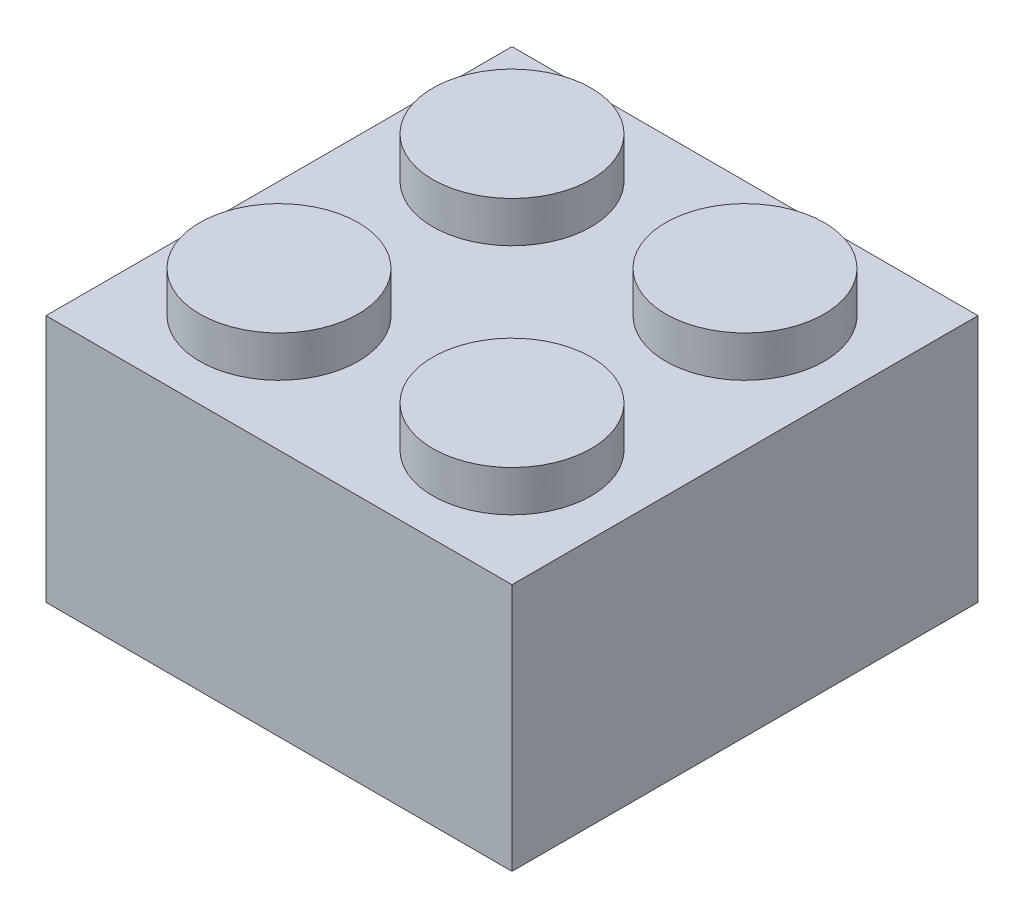
SolidWorks part; units mm, degrees
ref_plane "Front Plane" through (0, 0, 0) normal (0, 0, 1) x (1, 0, 0)
ref_plane "Top Plane" through (0, 0, 0) normal (0, 1, 0) x (1, 0, 0)
ref_plane "Right Plane" through (0, 0, 0) normal (1, 0, 0) x (0, 0, -1)
sketch "Sketch1" plane through (0, 0, 0) normal (0, 1, 0) x (1, 0, 0)
  line L1 (7.9375, 7.9375) -> (-7.9375, 7.9375)
  line L2 (7.9375, 7.9375) -> (7.9375, -7.9375)
  line L3 (7.9375, -7.9375) -> (-7.9375, -7.9375)
  line L4 (-7.9375, 7.9375) -> (-7.9375, -7.9375)
  line L5 (7.9375, 7.9375) -> (-7.9375, -7.9375) construction
  line L6 (7.9375, -7.9375) -> (-7.9375, 7.9375) construction
  point P0 (0, 0)
  dimension "D1" = 15.875
extrude "Boss-Extrude1" add sketch "Sketch1" along normal mid plane 8.4582
sketch "Sketch2" plane through (0, -4.2291, 0) normal (0, -1, 0) x (1, 0, 0)
  line L8 (-6.6675, 6.6675) -> (-6.6675, -6.6675)
  line L9 (-6.6675, -6.6675) -> (6.6675, -6.6675)
  line L10 (6.6675, -6.6675) -> (6.6675, 6.6675)
  line L11 (6.6675, 6.6675) -> (-6.6675, 6.6675)
  line L12 (-6.6675, 6.6675) -> (-6.6675, -6.6675)
  line L13 (-6.6675, -6.6675) -> (6.6675, -6.6675)
  line L14 (6.6675, -6.6675) -> (6.6675, 6.6675)
  line L15 (6.6675, 6.6675) -> (-6.6675, 6.6675)
  circle A0 centre (0, 0) radius 3.175
  circle A1 centre (0, 0) radius 2.413
  dimension "D2" = 6.35
  dimension "D3" = 4.826
  dimension "D1" = 1.27
extrude "Cut-Extrude1" cut sketch "Sketch2" against normal offset from surface (7.1882 mm away) 1.27 contours L14 L15 L12 L13 A0 | A1 up to face at (0, 4.2291, 0)
sketch "Sketch3" plane through (0, 4.2291, 0) normal (0, 1, 0) x (1, 0, 0)
  line L0 (7.9375, -7.9375) -> (7.9375, 7.9375) construction
  line L1 (-7.9375, -7.9375) -> (7.9375, -7.9375) construction
  circle A0 centre (3.9688, -3.9687) radius 2.6987
  dimension "D1" = 5.3975
  dimension "D2" = 3.9688
  dimension "D3" = 3.9688
extrude "Boss-Extrude2" add sketch "Sketch3" along normal blind 1.397
pattern_linear "LPattern1" count 2 spacing 7.9375 along (-1, 0, 0) count 2 spacing 7.9375 along (0, 0, -1) of "Boss-Extrude2"
